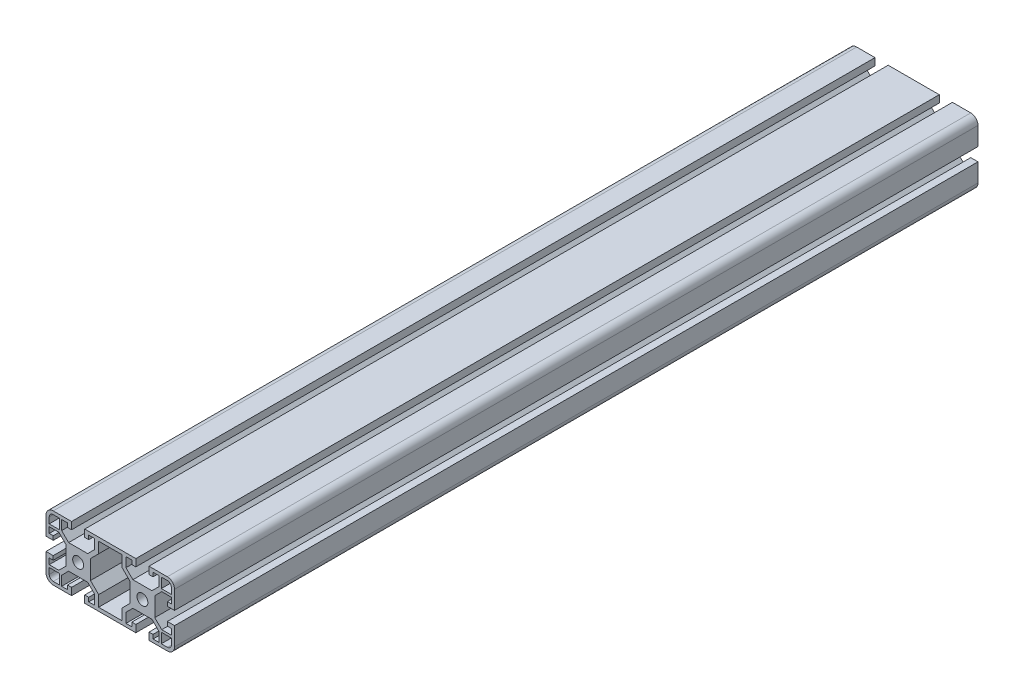
SolidWorks part; units mm, degrees
ref_plane "Front Plane" through (0, 0, 0) normal (0, 0, 1) x (1, 0, 0)
ref_plane "Top Plane" through (0, 0, 0) normal (0, 1, 0) x (1, 0, 0)
ref_plane "Right Plane" through (0, 0, 0) normal (1, 0, 0) x (0, 0, -1)
sketch "Sketch1" plane through (0, 0, 0) normal (0, 0, 1) x (1, 0, 0)
  line L0 (0, 17.8) -> (0, -17.8) construction
  line B0 (38, -15.5) -> (38, -11.75)
  line B1 (38, -11.75) -> (31.75, -11.75)
  line B2 (31.75, -11.75) -> (31.75, -18)
  line B3 (31.75, -18) -> (35.5, -18)
  arc B4 (35.5, -18) -> (38, -15.5) centre (35.5, -15.5) ccw
  line B5 (-38, 15.5) -> (-38, 11.75)
  line B6 (-38, 11.75) -> (-31.75, 11.75)
  line B7 (-31.75, 11.75) -> (-31.75, 18)
  line B8 (-31.75, 18) -> (-35.5, 18)
  arc B9 (-35.5, 18) -> (-38, 15.5) centre (-35.5, 15.5) ccw
  line B10 (24.1, -20) -> (35.5, -20)
  arc B11 (35.5, -20) -> (40, -15.5) centre (35.5, -15.5) ccw
  line B12 (40, -15.5) -> (40, -4.1)
  line B13 (40, -4.1) -> (35.5, -4.1)
  line B14 (35.5, -4.1) -> (35.5, -6.6)
  line B15 (35.5, -6.6) -> (38, -6.6)
  line B16 (38, -6.6) -> (38, -10.25)
  line B17 (38, -10.25) -> (32.0178, -10.25)
  line B18 (32.0178, -10.25) -> (27.7, -5.9322)
  line B19 (27.7, -5.9322) -> (27.7, 5.9322)
  line B20 (27.7, 5.9322) -> (32.0178, 10.25)
  line B21 (32.0178, 10.25) -> (38, 10.25)
  line B22 (38, 10.25) -> (38, 6.6)
  line B23 (38, 6.6) -> (35.5, 6.6)
  line B24 (35.5, 6.6) -> (35.5, 4.1)
  line B25 (35.5, 4.1) -> (40, 4.1)
  line B26 (40, 4.1) -> (40, 15.5)
  arc B27 (40, 15.5) -> (35.5, 20) centre (35.5, 15.5) ccw
  line B28 (35.5, 20) -> (24.1, 20)
  line B29 (24.1, 20) -> (24.1, 15.5)
  line B30 (24.1, 15.5) -> (26.6, 15.5)
  line B31 (26.6, 15.5) -> (26.6, 18)
  line B32 (26.6, 18) -> (30.25, 18)
  line B33 (30.25, 18) -> (30.25, 12.0178)
  line B34 (30.25, 12.0178) -> (25.9322, 7.7)
  line B35 (25.9322, 7.7) -> (14.0678, 7.7)
  line B36 (14.0678, 7.7) -> (9.75, 12.0178)
  line B37 (9.75, 12.0178) -> (9.75, 18)
  line B38 (9.75, 18) -> (13.4, 18)
  line B39 (13.4, 18) -> (13.4, 15.5)
  line B40 (13.4, 15.5) -> (15.9, 15.5)
  line B41 (15.9, 15.5) -> (15.9, 20)
  line B42 (15.9, 20) -> (-15.9, 20)
  line B43 (-15.9, 20) -> (-15.9, 15.5)
  line B44 (-15.9, 15.5) -> (-13.4, 15.5)
  line B45 (-13.4, 15.5) -> (-13.4, 18)
  line B46 (-13.4, 18) -> (-9.75, 18)
  line B47 (-9.75, 18) -> (-9.75, 12.0178)
  line B48 (-9.75, 12.0178) -> (-14.0678, 7.7)
  line B49 (-14.0678, 7.7) -> (-25.9322, 7.7)
  line B50 (-25.9322, 7.7) -> (-30.25, 12.0178)
  line B51 (-30.25, 12.0178) -> (-30.25, 18)
  line B52 (-30.25, 18) -> (-26.6, 18)
  line B53 (-26.6, 18) -> (-26.6, 15.5)
  line B54 (-26.6, 15.5) -> (-24.1, 15.5)
  line B55 (-24.1, 15.5) -> (-24.1, 20)
  line B56 (-24.1, 20) -> (-35.5, 20)
  arc B57 (-35.5, 20) -> (-40, 15.5) centre (-35.5, 15.5) ccw
  line B58 (-40, 15.5) -> (-40, 4.1)
  line B59 (-40, 4.1) -> (-35.5, 4.1)
  line B60 (-35.5, 4.1) -> (-35.5, 6.6)
  line B61 (-35.5, 6.6) -> (-38, 6.6)
  line B62 (-38, 6.6) -> (-38, 10.25)
  line B63 (-38, 10.25) -> (-32.0178, 10.25)
  line B64 (-32.0178, 10.25) -> (-27.7, 5.9322)
  line B65 (-27.7, 5.9322) -> (-27.7, -5.9322)
  line B66 (-27.7, -5.9322) -> (-32.0178, -10.25)
  line B67 (-32.0178, -10.25) -> (-38, -10.25)
  line B68 (-38, -10.25) -> (-38, -6.6)
  line B69 (-38, -6.6) -> (-35.5, -6.6)
  line B70 (-35.5, -6.6) -> (-35.5, -4.1)
  line B71 (-35.5, -4.1) -> (-40, -4.1)
  line B72 (-40, -4.1) -> (-40, -15.5)
  arc B73 (-40, -15.5) -> (-35.5, -20) centre (-35.5, -15.5) ccw
  line B74 (-35.5, -20) -> (-24.1, -20)
  line B75 (-24.1, -20) -> (-24.1, -15.5)
  line B76 (-24.1, -15.5) -> (-26.6, -15.5)
  line B77 (-26.6, -15.5) -> (-26.6, -18)
  line B78 (-26.6, -18) -> (-30.25, -18)
  line B79 (-30.25, -18) -> (-30.25, -12.0178)
  line B80 (-30.25, -12.0178) -> (-25.9322, -7.7)
  line B81 (-25.9322, -7.7) -> (-14.0678, -7.7)
  line B82 (-14.0678, -7.7) -> (-9.75, -12.0178)
  line B83 (-9.75, -12.0178) -> (-9.75, -18)
  line B84 (-9.75, -18) -> (-13.4, -18)
  line B85 (-13.4, -18) -> (-13.4, -15.5)
  line B86 (-13.4, -15.5) -> (-15.9, -15.5)
  line B87 (-15.9, -15.5) -> (-15.9, -20)
  line B88 (-15.9, -20) -> (15.9, -20)
  line B89 (15.9, -20) -> (15.9, -15.5)
  line B90 (15.9, -15.5) -> (13.4, -15.5)
  line B91 (13.4, -15.5) -> (13.4, -18)
  line B92 (13.4, -18) -> (9.75, -18)
  line B93 (9.75, -18) -> (9.75, -12.0178)
  line B94 (9.75, -12.0178) -> (14.0678, -7.7)
  line B95 (14.0678, -7.7) -> (25.9322, -7.7)
  line B96 (25.9322, -7.7) -> (30.25, -12.0178)
  line B97 (30.25, -12.0178) -> (30.25, -18)
  line B98 (30.25, -18) -> (26.6, -18)
  line B99 (26.6, -18) -> (26.6, -15.5)
  line B100 (26.6, -15.5) -> (24.1, -15.5)
  line B101 (24.1, -15.5) -> (24.1, -20)
  line B102 (-7.25, -10.9822) -> (-7.25, -17.8)
  line B103 (-7.25, -17.8) -> (7.25, -17.8)
  line B104 (7.25, -17.8) -> (7.25, -10.9822)
  line B105 (7.25, -10.9822) -> (12.3, -5.9322)
  line B106 (12.3, -5.9322) -> (12.3, 5.9322)
  line B107 (12.3, 5.9322) -> (7.25, 10.9822)
  line B108 (7.25, 10.9822) -> (7.25, 17.8)
  line B109 (7.25, 17.8) -> (-7.25, 17.8)
  line B110 (-7.25, 17.8) -> (-7.25, 10.9822)
  line B111 (-7.25, 10.9822) -> (-12.3, 5.9322)
  line B112 (-12.3, 5.9322) -> (-12.3, -5.9322)
  line B113 (-12.3, -5.9322) -> (-7.25, -10.9822)
  circle B114 centre (-20, 0) radius 3.4
  circle B115 centre (20, 0) radius 3.4
  line B116 (-35.5, -18) -> (-31.75, -18)
  line B117 (-31.75, -18) -> (-31.75, -11.75)
  line B118 (-31.75, -11.75) -> (-38, -11.75)
  line B119 (-38, -11.75) -> (-38, -15.5)
  arc B120 (-38, -15.5) -> (-35.5, -18) centre (-35.5, -15.5) ccw
  line B121 (35.5, 18) -> (31.75, 18)
  line B122 (31.75, 18) -> (31.75, 11.75)
  line B123 (31.75, 11.75) -> (38, 11.75)
  line B124 (38, 11.75) -> (38, 15.5)
  arc B125 (38, 15.5) -> (35.5, 18) centre (35.5, 15.5) ccw
sketch_block_instance "S8-4080-1"
sketch_block "S8-4080"
extrude "Boss-Extrude1" add sketch "Sketch1" along normal blind 500
